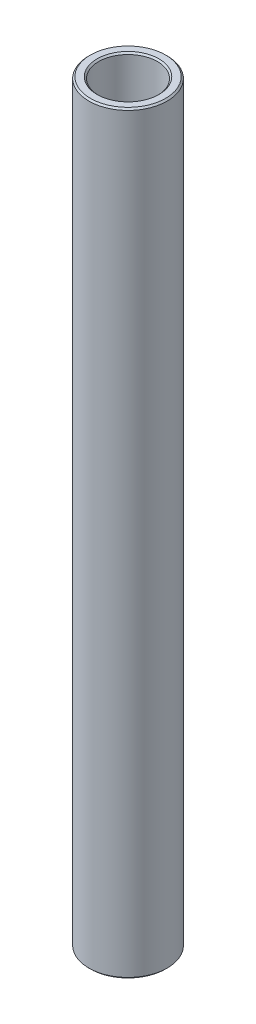
SolidWorks part; units mm, degrees
ref_plane "Front Plane" through (0, 0, 0) normal (0, 0, 1) x (1, 0, 0)
ref_plane "Top Plane" through (0, 0, 0) normal (0, 1, 0) x (1, 0, 0)
ref_plane "Right Plane" through (0, 0, 0) normal (1, 0, 0) x (0, 0, -1)
sketch "Sketch1" plane through (0, 0, 0) normal (0, 0, 1) x (1, 0, 0)
  line L0 (4.7625, 131.7624) -> (4.7625, 253.9999)
  line L1 (4.7625, 253.9999) -> (6.35, 253.9999)
  line L2 (6.35, 253.9999) -> (6.35, 131.7624)
  line L3 (6.35, 131.7624) -> (4.7625, 131.7624)
  line L4 (120.0875, 142.0811) -> (10.0875, 142.0811) construction
  line L6 (0, 122.2374) -> (0, 263.5249) construction
  dimension "D1" = 9.525
  dimension "D2" = 9.525
  dimension "D3" = 12.7
  dimension "D4" = 9.525
revolve "Revolve1" add sketch "Sketch1" angle 360 about L6
chamfer "Chamfer1" distance 0.254 angle 45 4 edges at (6.35, 253.9999, 0) (4.7625, 253.9999, 0) (4.7625, 131.7624, 0) (6.35, 131.7624, 0)
equation "\"D4@Sketch1\"=\"D1@Sketch1\""
